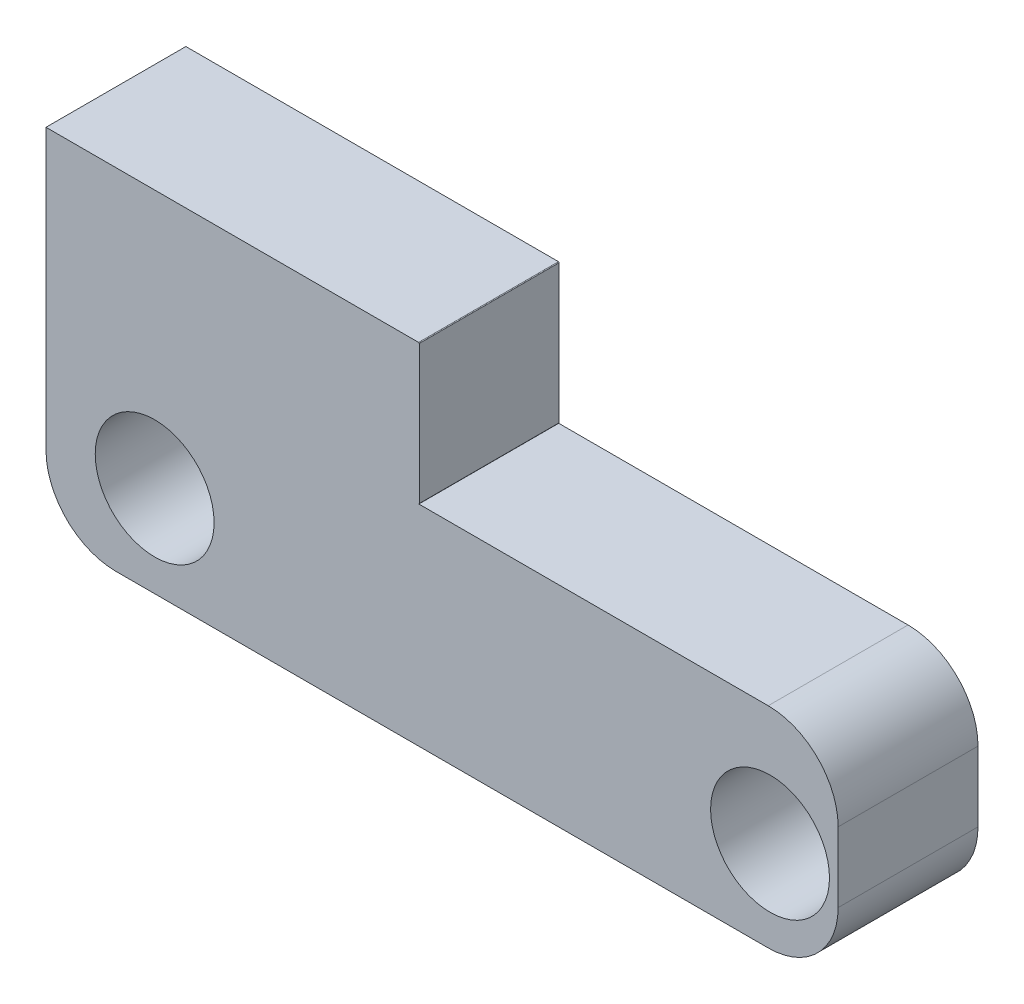
SolidWorks part; units mm, degrees
ref_plane "Front Plane" through (0, 0, 0) normal (0, 0, 1) x (1, 0, 0)
ref_plane "Top Plane" through (0, 0, 0) normal (0, 1, 0) x (1, 0, 0)
ref_plane "Right Plane" through (0, 0, 0) normal (1, 0, 0) x (0, 0, -1)
sketch "Esboço1" plane through (0, 0, 0) normal (0, 0, 1) x (1, 0, 0)
  line L0 (-26.6892, 0) -> (-26.6892, 10)
  line L13 (-26.6892, 0) -> (-0.05, 0)
  line L14 (0, 0.05) -> (0, 9.95)
  line L15 (-0.05, 10) -> (-26.6892, 10)
  arc A13 (-0.05, 0) -> (0, 0.05) centre (-0.05, 0.05) ccw
  arc A14 (0, 9.95) -> (-0.05, 10) centre (-0.05, 9.95) ccw
extrude "Ressalto-extrusão1" add sketch "Esboço1" along normal blind 10
sketch "Esboço2" plane through (0, 0, 0) normal (0, -1, 0) x (1, 0, 0)
  line L8 (-26.6892, 0) -> (-0.05, 0)
  line L9 (-0.05, 0) -> (-0.05, 10)
  line L10 (-0.05, 10) -> (-26.6892, 10)
  line L11 (-26.6892, 10) -> (-26.6892, 0)
  line L12 (-26.6892, 0) -> (-0.05, 0)
  line L13 (-0.05, 0) -> (-0.05, 10)
  line L14 (-0.05, 10) -> (-26.6892, 10)
  line L15 (-26.6892, 10) -> (-26.6892, 0)
  dimension "D1" = 0
extrude "Ressalto-extrusão2" add sketch "Esboço2" along normal blind 15
sketch "Esboço3" plane through (-0.05, 0, 0) normal (1, 0, 0) x (0, 0, -1)
  line L8 (0, 0) -> (-10, 0)
  line L9 (-10, 0) -> (-10, -15)
  line L10 (-10, -15) -> (0, -15)
  line L11 (0, -15) -> (0, 0)
  line L12 (0, 0) -> (-10, 0)
  line L13 (-10, 0) -> (-10, -15)
  line L14 (-10, -15) -> (0, -15)
  line L15 (0, -15) -> (0, 0)
  dimension "D1" = 0
extrude "Ressalto-extrusão3" add sketch "Esboço3" along normal blind 30
sketch "Esboço4" plane through (0, 0, 0) normal (0, 0, -1) x (-1, 0, 0)
  circle A2 centre (-25.08, -8.4733) radius 4.25
  circle A3 centre (-25.08, -8.4733) radius 4.25
  circle A5 centre (18.92, -8.4733) radius 4.25
  circle A6 centre (18.92, -8.4733) radius 4.25
  dimension "D1" = 0
  dimension "D2" = 0
extrude "Corte-extrusão1" cut sketch "Esboço4" against normal blind 30
fillet "Filete1" radius 5 3 edges at (-26.6892, -15, 5) (29.95, -15, 5) (29.95, 0, 5)
